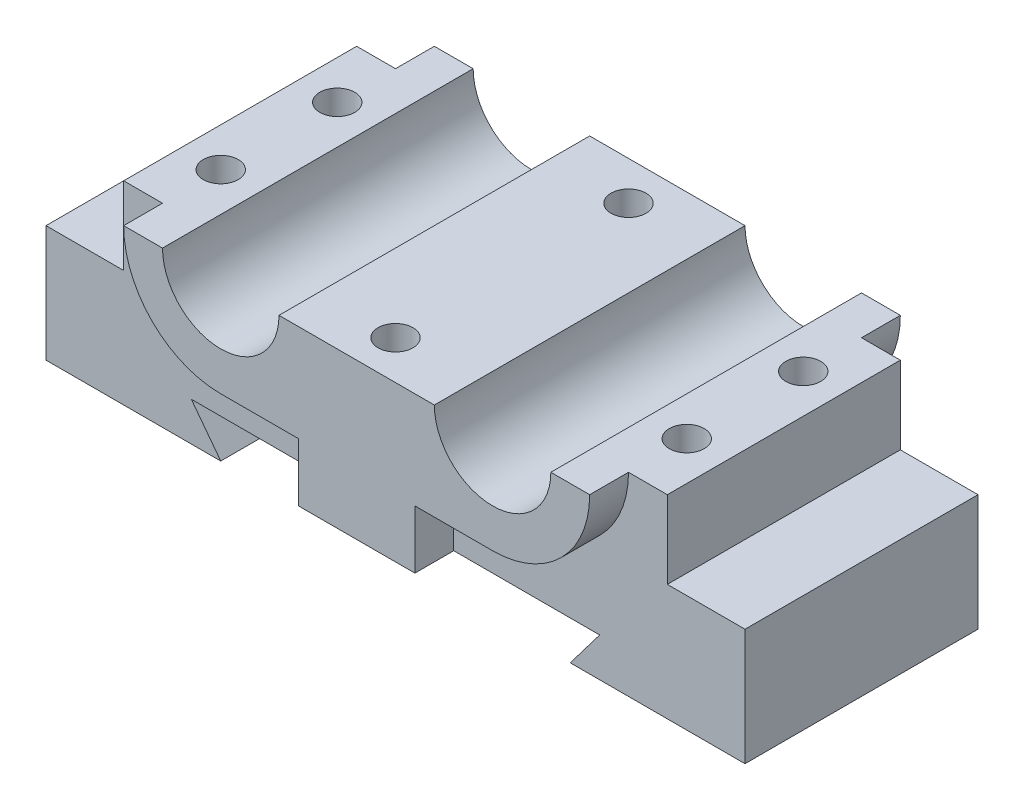
SolidWorks part; units mm, degrees
ref_plane "Front Plane" through (0, 0, 0) normal (0, 0, 1) x (1, 0, 0)
ref_plane "Top Plane" through (0, 0, 0) normal (0, 1, 0) x (1, 0, 0)
ref_plane "Right Plane" through (0, 0, 0) normal (1, 0, 0) x (0, 0, -1)
sketch "Sketch1" plane through (0, 0, 0) normal (0, 1, 0) x (1, 0, 0)
  line L1 (-45, -15) -> (45, -15)
  line L2 (-45, -15) -> (-45, 15)
  line L3 (-45, 15) -> (45, 15)
  line L4 (45, -15) -> (45, 15)
  line L5 (0, 15) -> (0, -15) construction
  line L6 (-45, 0) -> (45, 0) construction
  point P0 (0, 0)
extrude "Boss-Extrude1" add sketch "Sketch1" along normal mid plane 15
sketch "Sketch2" plane through (0, 7.5, 0) normal (0, 1, 0) x (1, 0, 0)
  line L1 (-45, -15) -> (45, -15) construction
  line L2 (45, 15) -> (-45, 15) construction
  line L3 (-35, -15) -> (35, -15)
  line L4 (-35, -15) -> (-35, 15)
  line L5 (-35, 15) -> (35, 15)
  line L6 (35, -15) -> (35, 15)
extrude "Boss-Extrude2" add sketch "Sketch2" along normal blind 10
sketch "Sketch3" plane through (0, 0, 15) normal (0, 0, 1) x (1, 0, 0)
  line L0 (-26.2868, -2.5) -> (26.2868, -2.5)
  line L1 (-45, -7.5) -> (45, -7.5) construction
  line L2 (22.5, -7.5) -> (26.2868, -2.5)
  line L3 (-22.5, -7.5) -> (22.5, -7.5)
  line L5 (-22.5, -7.5) -> (-26.2868, -2.5)
  dimension "D2" = 5
extrude "Cut-Extrude1" cut sketch "Sketch3" against normal through all
sketch "Sketch4" plane through (0, 0, 15) normal (0, 0, 1) x (1, 0, 0)
  line L0 (-7.5, -2.5) -> (7.5, -2.5)
  line L1 (-35, 17.5) -> (35, 17.5) construction
  line L2 (26.2868, -2.5) -> (-26.2868, -2.5) construction
  line L3 (-25, 17.5) -> (-30, 17.5)
  line L4 (-10, 17.5) -> (10.0749, 17.5)
  line L5 (-17.5, 5) -> (-7.5, 5)
  line L6 (-7.5, -2.5) -> (-7.5, 5)
  line L8 (7.5, 5) -> (7.5, -2.5)
  line L9 (7.5, -2.5) -> (7.517, -2.5657)
  line L10 (7.5, 5) -> (17.5, 5)
  arc A0 (-25, 17.5) -> (-10, 17.5) centre (-17.5, 17.5) ccw
  arc A1 (10, 17.5) -> (25, 17.5) centre (17.5, 17.5) ccw
  arc A2 (-30, 17.5) -> (-17.5, 5) centre (-17.5, 17.5) ccw
  arc A3 (17.5, 5) -> (30, 17.5) centre (17.5, 17.5) ccw
  point P5 (0, 17.5)
  point P20 (0, -2.5)
  line M4 (-26.2868, -2.5) -> (26.2868, -2.5)
  line M10 (35, 17.5) -> (-35, 17.5)
  dimension "D1" = 35
  dimension "D3" = 17.5
extrude "Boss-Extrude3" add sketch "Sketch4" along normal blind 5 and the other way blind 35 contours L10 A3 A1 L4 A0 A2 L5 L6 L8 M10 M4
sketch "Sketch6" plane through (0, 0, 15) normal (0, 0, 1) x (1, 0, 0)
  line L0 (10, 17.5) -> (25, 17.5) construction
  line L1 (-25, 17.5) -> (-10, 17.5)
  line L2 (10, 17.5) -> (25, 17.5)
  arc A0 (-25, 17.5) -> (-10, 17.5) centre (-17.5, 17.5) ccw
  arc A1 (10, 17.5) -> (25, 17.5) centre (17.5, 17.5) ccw
  arc A2 (10, 17.5) -> (25, 17.5) centre (17.5, 17.5) ccw construction
extrude "Cut-Extrude2" cut sketch "Sketch6" against normal blind 30
sketch "Sketch7" plane through (0, 17.5, 0) normal (0, 1, 0) x (1, 0, 0)
  circle A0 centre (0, 15) radius 2.25
  circle A1 centre (0, -15) radius 2.25
  circle A2 centre (-30, 7.5) radius 2.25
  circle A3 centre (-30, -7.5) radius 2.25
  circle A4 centre (30, -7.5) radius 2.25
  circle A5 centre (30, 7.5) radius 2.25
extrude "Cut-Extrude3" cut sketch "Sketch7" against normal blind 15
